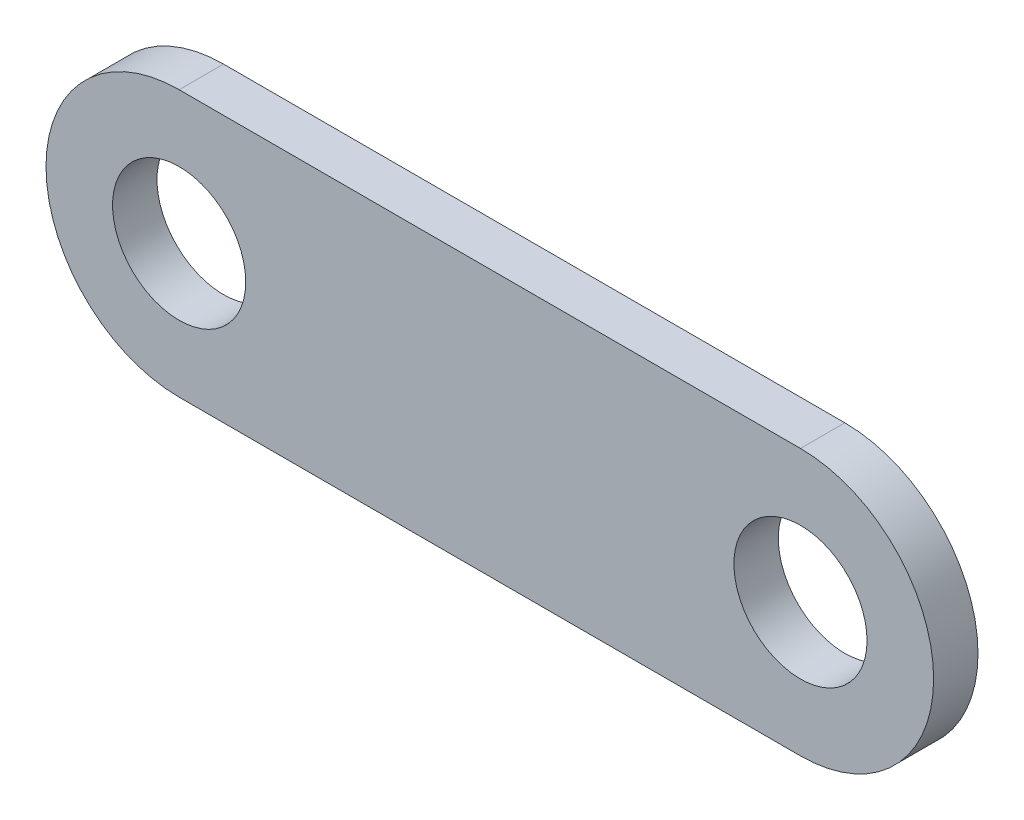
SolidWorks part; units mm, degrees
material "Cast Alloy Steel"
ref_plane "Front Plane" through (0, 0, 0) normal (0, 0, 1) x (1, 0, 0)
ref_plane "Top Plane" through (0, 0, 0) normal (0, 1, 0) x (1, 0, 0)
ref_plane "Right Plane" through (0, 0, 0) normal (1, 0, 0) x (0, 0, -1)
other "Configuration Table"
sketch "Sketch1" plane through (0, 0, 0) normal (0, 0, 1) x (1, 0, 0)
  line L0 (0, 0) -> (-44.45, 0) construction
  line L1 (0, -9.525) -> (-44.45, -9.525)
  line L2 (0, 9.525) -> (-44.45, 9.525)
  arc A0 (0, -9.525) -> (0, 9.525) centre (0, 0) ccw
  arc A1 (-44.45, 9.525) -> (-44.45, -9.525) centre (-44.45, 0) ccw
  circle A3 centre (-44.45, 0) radius 4.7625
  circle A4 centre (0, 0) radius 4.7625
  point P3 (-22.225, 0)
  dimension "D1" = 9.525
  dimension "D3" = 9.525
  dimension "D2" = 44.45
extrude "Boss-Extrude1" add sketch "Sketch1" against normal blind 3.175
